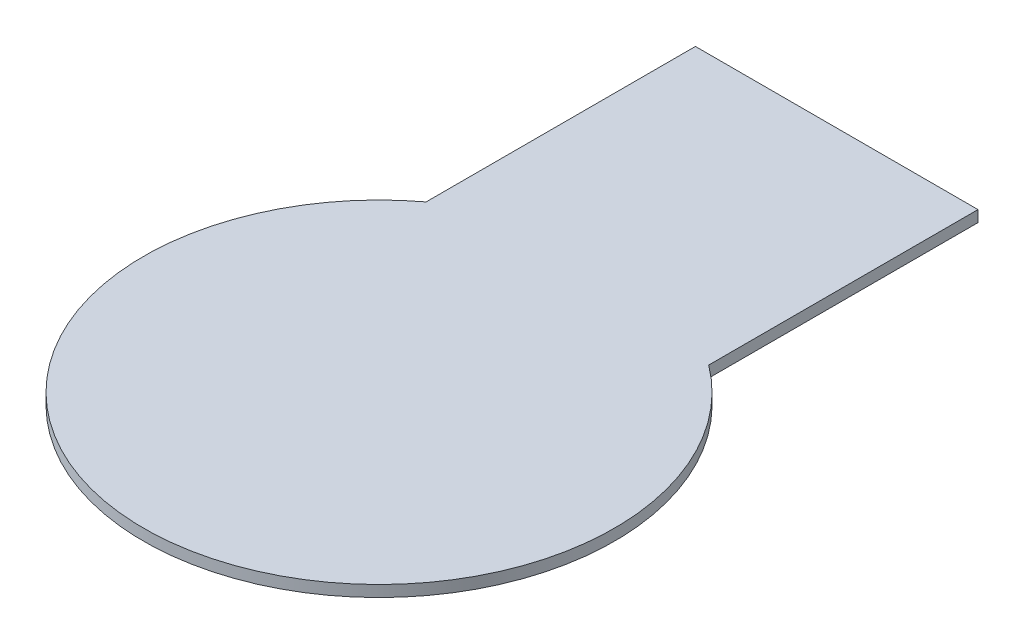
SolidWorks part; units mm, degrees
ref_plane "Front Plane" through (0, 0, 0) normal (0, 0, 1) x (1, 0, 0)
ref_plane "Top Plane" through (0, 0, 0) normal (0, 1, 0) x (1, 0, 0)
ref_plane "Right Plane" through (0, 0, 0) normal (1, 0, 0) x (0, 0, -1)
sketch "Sketch1" plane through (0, 0, 0) normal (0, 1, 0) x (1, 0, 0)
  line L1 (-7.5, 24.2955) -> (7.5, 24.2955)
  line L2 (-7.5, 24.2955) -> (-7.5, 0.7045)
  line L3 (-7.5, 0.7045) -> (7.5, 0.7045)
  line L4 (7.5, 24.2955) -> (7.5, 0.7045)
  line L5 (0, 0.7045) -> (0, 24.2955) construction
  line L6 (-7.5, 12.5) -> (7.5, 12.5) construction
  circle A0 centre (0, 0) radius 12.5
  point P3 (0, 12.5)
  dimension "D1" = 25
  dimension "D2" = 15
extrude "Boss-Extrude1" add sketch "Sketch1" along normal blind 0.6 contours L2 A0 L4 L3 | L4 A0 L2 L3 | A0 L4 L1 L2
